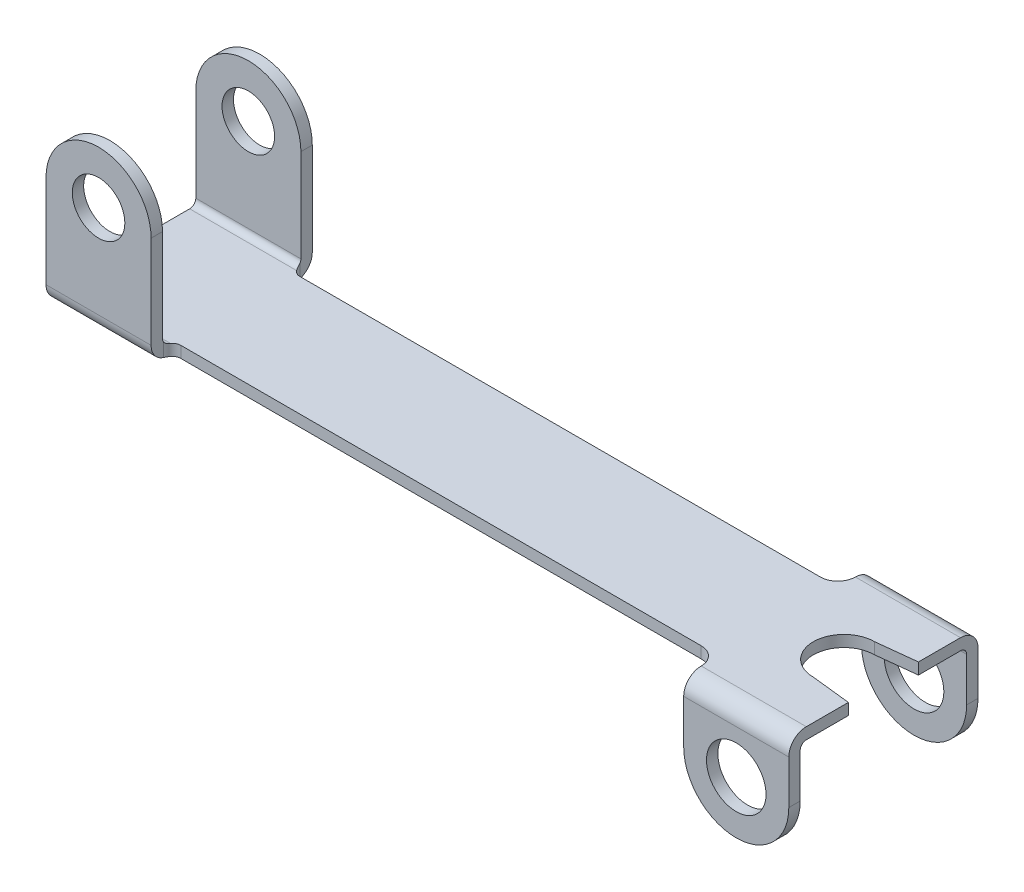
SolidWorks part; units mm, degrees
material "Zinc Alloy 7; AG40B; Zn-4Al-0.015Mg"
ref_plane "Front Plane" through (0, 0, 0) normal (0, 0, 1) x (1, 0, 0)
ref_plane "Top Plane" through (0, 0, 0) normal (0, 1, 0) x (1, 0, 0)
ref_plane "Right Plane" through (0, 0, 0) normal (1, 0, 0) x (0, 0, -1)
sketch "Sketch1" plane through (0, 0, 0) normal (0, 1, 0) x (1, 0, 0)
  line L0 (7.8, 2.7) -> (10.8, 2.7)
  line L1 (-7.55, 1.7) -> (7.3, 1.7)
  line L2 (-10.8, 2.3) -> (-10.8, -2.3)
  line L3 (-7.55, -1.7) -> (7.3, -1.7)
  line L4 (10.8, 2.7) -> (10.8, 1)
  line L5 (10.8, -2.7) -> (7.8, -2.7)
  line L6 (7.8, 2.7) -> (7.8, 2.2)
  line L7 (7.8, -2.2) -> (7.8, -2.7)
  line L8 (-10.8, 2.3) -> (-7.8, 2.3)
  line L9 (-10.8, -2.3) -> (-7.8, -2.3)
  line L10 (-7.8, 2.3) -> (-7.8, 1.95)
  line L11 (-7.8, -1.95) -> (-7.8, -2.3)
  line L12 (9.675, 0.875) -> (10.8, 1)
  line L13 (9.675, -0.875) -> (10.8, -1)
  line L14 (10.8, -1) -> (10.8, -2.7)
  arc A0 (-7.8, 1.95) -> (-7.55, 1.7) centre (-7.55, 1.95) ccw
  arc A1 (-7.8, -1.95) -> (-7.55, -1.7) centre (-7.55, -1.95) cw
  arc A2 (7.8, 2.2) -> (7.3, 1.7) centre (7.3, 2.2) cw
  arc A3 (7.8, -2.2) -> (7.3, -1.7) centre (7.3, -2.2) ccw
  arc A4 (9.675, 0.875) -> (9.675, -0.875) centre (9.675, 0) ccw
  point P17 (-7.8, -1.7)
  point P22 (7.8, -1.7)
  dimension "D12" = 0.25
  dimension "D13" = 0.5
  dimension "D14" = 1.75
  dimension "D2" = 10.8
  dimension "D3" = 3.4
  dimension "D4" = 1.7
  dimension "D5" = 5.4
  dimension "D6" = 2.7
  dimension "D7" = 3
  dimension "D8" = 4.6
  dimension "D9" = 2.3
  dimension "D10" = 3
  dimension "D11" = 21.6
  dimension "D15" = 1.125
  dimension "D16" = 2
  dimension "D17" = 1
extrude "Extrude1" add sketch "Sketch1" along normal mid plane 0.325
sketch "Sketch2" plane through (0, -0.1625, 0) normal (0, -1, 0) x (1, 0, 0)
  line L0 (7.8, 2.7) -> (10.8, 2.7) construction
  line L1 (7.8, 2.7) -> (10.8, 2.7)
  line L2 (7.8, 2.7) -> (7.8, 2.375)
  line L3 (7.8, 2.375) -> (10.8, 2.375)
  line L4 (10.8, 2.7) -> (10.8, 2.375)
  line L5 (7.8, -2.7) -> (10.8, -2.7)
  line L6 (7.8, -2.7) -> (7.8, -2.375)
  line L7 (7.8, -2.375) -> (10.8, -2.375)
  line L8 (10.8, -2.7) -> (10.8, -2.375)
  line L9 (10.8, 2.7) -> (10.8, 1) construction
  line L10 (7.8, 2.2) -> (7.8, 2.7) construction
  line L11 (10.8, -2.7) -> (7.8, -2.7) construction
  line L12 (10.8, -1) -> (10.8, -2.7) construction
  line L13 (7.8, -2.7) -> (7.8, -2.2) construction
  dimension "D1" = 2.375
  dimension "D2" = 2.375
extrude "Extrude2" add sketch "Sketch2" along normal blind 2.925
sketch "Sketch3" plane through (0, 0.1625, 0) normal (0, 1, 0) x (1, 0, 0)
  line L0 (-7.8, 2.3) -> (-10.8, 2.3) construction
  line L1 (-10.8, 2.3) -> (-7.8, 2.3)
  line L2 (-10.8, 2.3) -> (-10.8, 1.975)
  line L3 (-10.8, 1.975) -> (-7.8, 1.975)
  line L4 (-7.8, 2.3) -> (-7.8, 1.975)
  line L5 (-10.8, -2.3) -> (-7.8, -2.3)
  line L6 (-10.8, -2.3) -> (-10.8, -1.975)
  line L7 (-10.8, -1.975) -> (-7.8, -1.975)
  line L8 (-7.8, -2.3) -> (-7.8, -1.975)
  line L9 (-7.8, 1.95) -> (-7.8, 2.3) construction
  line L10 (-10.8, 2.3) -> (-10.8, -2.3) construction
  line L11 (-10.8, -2.3) -> (-7.8, -2.3) construction
  line L12 (-7.8, -2.3) -> (-7.8, -1.95) construction
  dimension "D1" = 0.325
  dimension "D2" = 0.325
extrude "Extrude3" add sketch "Sketch3" along normal blind 4.325
sketch "Sketch4" plane through (0, 0, 2.7) normal (0, 0, 1) x (1, 0, 0)
  line L0 (10.8, -3.0875) -> (7.8, -3.0875) construction
  line L1 (7.8, 0.1625) -> (7.8, -3.0875) construction
  line L2 (10.8, 0.1625) -> (10.8, -3.0875) construction
  line L3 (7.8, -1.5875) -> (7.8, -3.5875)
  line L4 (7.8, -3.5875) -> (10.8, -3.5875)
  line L5 (10.8, -3.5875) -> (10.8, -1.5875)
  line L7 (-10.8, 4.4875) -> (-7.8, 4.4875) construction
  line L8 (-7.8, 4.4875) -> (-7.8, -0.1625) construction
  line L9 (-10.8, 4.4875) -> (-10.8, -0.1625) construction
  line L10 (-10.8, 2.9875) -> (-10.8, 4.9875)
  line L11 (-10.8, 4.9875) -> (-7.8, 4.9875)
  line L12 (-7.8, 4.9875) -> (-7.8, 2.9875)
  line L13 (-7.8, 2.9875) -> (-8.5828, 3.2068)
  arc A0 (7.8, -1.5875) -> (10.8, -1.5875) centre (9.3, -1.5875) ccw
  circle A1 centre (9.3, -1.5875) radius 0.85
  arc A2 (-7.8, 2.9875) -> (-10.8, 2.9875) centre (-9.3, 2.9875) ccw
  circle A3 centre (-9.3, 2.9875) radius 0.75
  dimension "D1" = 1.7
  dimension "D4" = 1.5
  dimension "D2" = 2
  dimension "D3" = 2
extrude "Extrude4" cut sketch "Sketch4" against normal through all
fillet "Fillet1" radius 0.5 4 edges at (-9.3, -0.1625, -2.3) (-9.3, -0.1625, 2.3) (9.3, 0.1625, -2.7) (9.3, 0.1625, 2.7)
fillet "Fillet2" radius 0.175 4 edges at (9.3, -0.1625, -2.375) (-9.3, 0.1625, 1.975)
